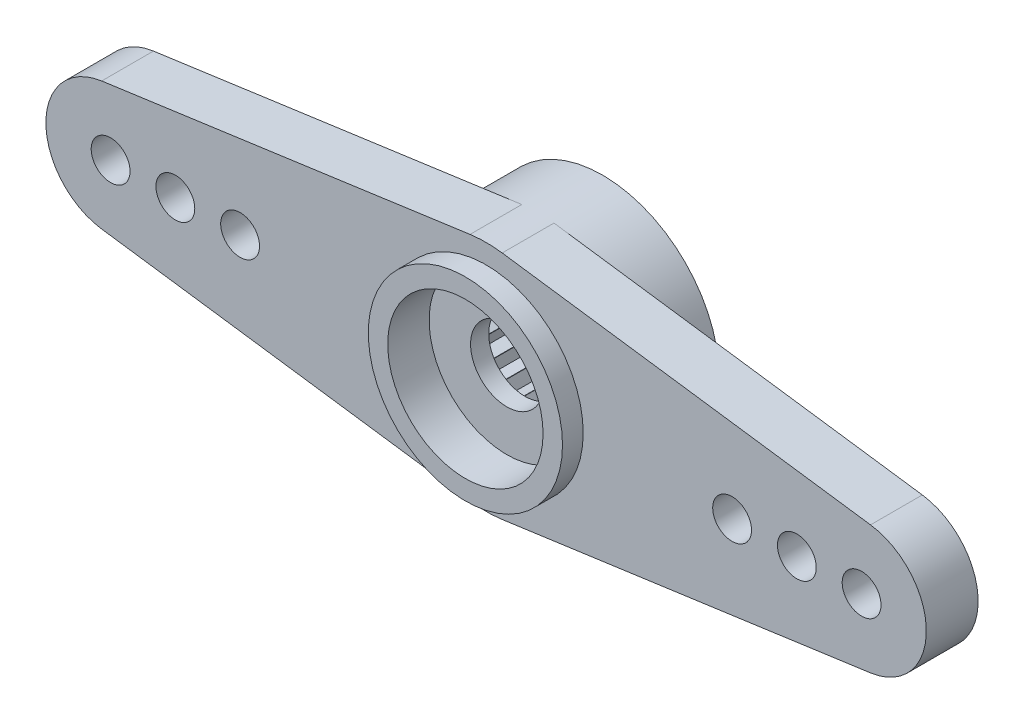
SolidWorks part; units mm, degrees
ref_plane "Face" through (0, 0, 0) normal (0, 0, 1) x (1, 0, 0)
ref_plane "Dessus" through (0, 0, 0) normal (0, 1, 0) x (1, 0, 0)
ref_plane "Droite" through (0, 0, 0) normal (1, 0, 0) x (0, 0, -1)
sketch "Esquisse1" plane through (0, 0, 0) normal (0, 0, 1) x (1, 0, 0)
  circle A0 centre (0, 0) radius 4.5
  line B0 (2.0116, -1.5509) -> (2.0116, -2.0116)
  line B1 (0.3258, 2.519) -> (0, 2.8448)
  line B2 (0.3373, 2.5175) -> (0.3258, 2.519)
  line B3 (0.7363, 2.7479) -> (0.3373, 2.5175)
  line B4 (0.9666, 2.3489) -> (0.7363, 2.7479)
  line B5 (0.9774, 2.3444) -> (0.9666, 2.3489)
  line B6 (1.4224, 2.4637) -> (0.9774, 2.3444)
  line B7 (1.5416, 2.0186) -> (1.4224, 2.4637)
  line B8 (1.5509, 2.0116) -> (1.5416, 2.0186)
  line B9 (2.0116, 2.0116) -> (1.5509, 2.0116)
  line B10 (2.0116, 1.5509) -> (2.0116, 2.0116)
  line B11 (2.0186, 1.5416) -> (2.0116, 1.5509)
  line B12 (2.4637, 1.4224) -> (2.0186, 1.5416)
  line B13 (2.3444, 0.9774) -> (2.4637, 1.4224)
  line B14 (2.3489, 0.9666) -> (2.3444, 0.9774)
  line B15 (2.7479, 0.7363) -> (2.3489, 0.9666)
  line B16 (2.5175, 0.3373) -> (2.7479, 0.7363)
  line B17 (2.519, 0.3258) -> (2.5175, 0.3373)
  line B18 (2.8448, 0) -> (2.519, 0.3258)
  line B19 (2.519, -0.3258) -> (2.8448, 0)
  line B20 (2.5175, -0.3373) -> (2.519, -0.3258)
  line B21 (2.7479, -0.7363) -> (2.5175, -0.3373)
  line B22 (2.3489, -0.9666) -> (2.7479, -0.7363)
  line B23 (2.3444, -0.9774) -> (2.3489, -0.9666)
  line B24 (2.4637, -1.4224) -> (2.3444, -0.9774)
  line B25 (2.0186, -1.5416) -> (2.4637, -1.4224)
  line B26 (2.0116, -1.5509) -> (2.0186, -1.5416)
  line B27 (1.5509, -2.0116) -> (2.0116, -2.0116)
  line B28 (1.5416, -2.0186) -> (1.5509, -2.0116)
  line B29 (1.4224, -2.4637) -> (1.5416, -2.0186)
  line B30 (0.9774, -2.3444) -> (1.4224, -2.4637)
  line B31 (0.9666, -2.3489) -> (0.9774, -2.3444)
  line B32 (0.7363, -2.7479) -> (0.9666, -2.3489)
  line B33 (0.3373, -2.5175) -> (0.7363, -2.7479)
  line B34 (0.3258, -2.519) -> (0.3373, -2.5175)
  line B35 (0, -2.8448) -> (0.3258, -2.519)
  line B36 (-0.3258, -2.519) -> (0, -2.8448)
  line B37 (-0.3373, -2.5175) -> (-0.3258, -2.519)
  line B38 (-0.7363, -2.7479) -> (-0.3373, -2.5175)
  line B39 (-0.9666, -2.3489) -> (-0.7363, -2.7479)
  line B40 (-0.9774, -2.3444) -> (-0.9666, -2.3489)
  line B41 (-1.4224, -2.4637) -> (-0.9774, -2.3444)
  line B42 (-1.5416, -2.0186) -> (-1.4224, -2.4637)
  line B43 (-1.5509, -2.0116) -> (-1.5416, -2.0186)
  line B44 (-2.0116, -2.0116) -> (-1.5509, -2.0116)
  line B45 (-2.0116, -1.5509) -> (-2.0116, -2.0116)
  line B46 (-2.0186, -1.5416) -> (-2.0116, -1.5509)
  line B47 (-2.4637, -1.4224) -> (-2.0186, -1.5416)
  line B48 (-2.3444, -0.9774) -> (-2.4637, -1.4224)
  line B49 (-2.3489, -0.9666) -> (-2.3444, -0.9774)
  line B50 (-2.7479, -0.7363) -> (-2.3489, -0.9666)
  line B51 (-2.5175, -0.3373) -> (-2.7479, -0.7363)
  line B52 (-2.519, -0.3258) -> (-2.5175, -0.3373)
  line B53 (-2.8448, 0) -> (-2.519, -0.3258)
  line B54 (-2.519, 0.3258) -> (-2.8448, 0)
  line B55 (-2.5175, 0.3373) -> (-2.519, 0.3258)
  line B56 (-2.7479, 0.7363) -> (-2.5175, 0.3373)
  line B57 (-2.3489, 0.9666) -> (-2.7479, 0.7363)
  line B58 (-2.3444, 0.9774) -> (-2.3489, 0.9666)
  line B59 (-2.4637, 1.4224) -> (-2.3444, 0.9774)
  line B60 (-2.0186, 1.5416) -> (-2.4637, 1.4224)
  line B61 (-2.0116, 1.5509) -> (-2.0186, 1.5416)
  line B62 (-2.0116, 2.0116) -> (-2.0116, 1.5509)
  line B63 (-1.5509, 2.0116) -> (-2.0116, 2.0116)
  line B64 (-1.5416, 2.0186) -> (-1.5509, 2.0116)
  line B65 (-1.4224, 2.4637) -> (-1.5416, 2.0186)
  line B66 (-0.9774, 2.3444) -> (-1.4224, 2.4637)
  line B67 (-0.9666, 2.3489) -> (-0.9774, 2.3444)
  line B68 (-0.7363, 2.7479) -> (-0.9666, 2.3489)
  line B69 (-0.3373, 2.5175) -> (-0.7363, 2.7479)
  line B70 (-0.3258, 2.519) -> (-0.3373, 2.5175)
  line B71 (0, 2.8448) -> (-0.3258, 2.519)
  dimension "D1" = 9
sketch_block_instance "Block1-1"
sketch_block "Block1"
extrude "Boss.-Extru.1" add sketch "Esquisse1" along normal blind 3
sketch "Esquisse2" plane through (0, 0, 3) normal (0, 0, 1) x (1, 0, 0)
  line L0 (-14.8448, 2.4761) -> (-0.6207, 4.457)
  line L1 (-14.8448, -2.4761) -> (-0.6207, -4.457)
  arc A0 (-14.8448, 2.4761) -> (-14.8448, -2.4761) centre (-14.5, 0) ccw
  circle A1 centre (0, 0) radius 4.5 construction
  arc A2 (-0.6207, 4.457) -> (-0.6207, -4.457) centre (0, 0) ccw
  circle A3 centre (-14.5, 0) radius 0.75
  circle A4 centre (-12, 0) radius 0.75
  circle A5 centre (-9.5, 0) radius 0.75
  dimension "D1" = 14.5
  dimension "D2" = 5
  dimension "D3" = 1.5
  dimension "D5" = 9.5
  dimension "D4" = 12
extrude "Boss.-Extru.2" add sketch "Esquisse2" along direction (0, 0, 1) on the side of the normal blind 1.5 and the other way blind 0.5
pattern_circular "Répétition circulaire1" count 2 over 360 about axis through (0, 0, 0) along (0, 0, 1) of "Boss.-Extru.2"
sketch "Esquisse5" plane through (0, 0, 3) normal (0, 0, 1) x (1, 0, 0)
  circle A0 centre (0, 0) radius 1.4
  circle A1 centre (0, 0) radius 4.5 construction
  circle A2 centre (0, 0) radius 4.5
  dimension "D1" = 2.8
extrude "Boss.-Extru.4" add sketch "Esquisse5" along normal blind 0.7
sketch "Esquisse6" plane through (0, 0, 3.7) normal (0, 0, 1) x (1, 0, 0)
  circle A0 centre (0, 0) radius 3
  circle A1 centre (0, 0) radius 4.5 construction
  circle A2 centre (0, 0) radius 4.5
  dimension "D1" = 6
extrude "Boss.-Extru.5" add sketch "Esquisse6" along normal up to surface (0.8 mm away) up to face at (-11.25, 0, 4.5)
sketch "Esquisse7" plane through (0, 0, 4.5) normal (0, 0, 1) x (1, 0, 0)
  circle A0 centre (0, 0) radius 3 construction
  circle A1 centre (0, 0) radius 3
  circle A2 centre (0, 0) radius 3.75
  dimension "D1" = 7.5
extrude "Boss.-Extru.6" add sketch "Esquisse7" along normal blind 0.8
